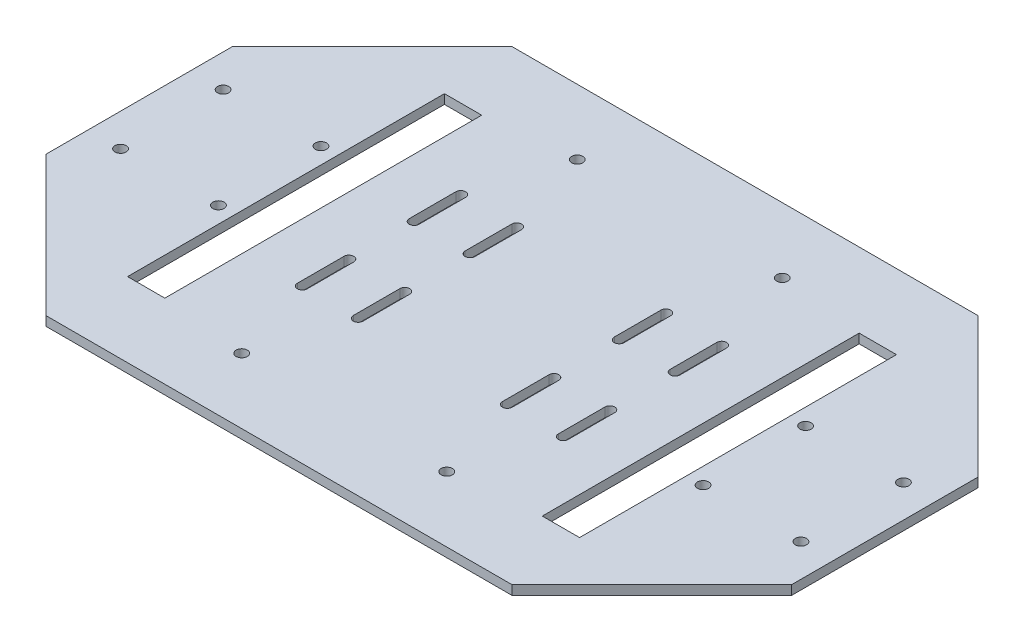
SolidWorks part; units mm, degrees
material "Pin"
ref_plane "Plan de face" through (0, 0, 0) normal (0, 0, 1) x (1, 0, 0)
ref_plane "Plan de dessus" through (0, 0, 0) normal (0, 1, 0) x (1, 0, 0)
ref_plane "Plan de droite" through (0, 0, 0) normal (1, 0, 0) x (0, 0, -1)
sketch "Esquisse1" plane through (0, 0, 0) normal (0, 1, 0) x (1, 0, 0)
  line L1 (0, 0) -> (160, 0)
  line L2 (0, 0) -> (0, 100)
  line L3 (0, 100) -> (160, 100)
  line L4 (160, 0) -> (160, 100)
  dimension "D1" = 100
  dimension "D2" = 160
extrude "Boss.-Extru.1" add sketch "Esquisse1" along normal blind 2
sketch "Esquisse2" plane through (0, 2, 0) normal (0, 1, 0) x (1, 0, 0)
  line L0 (30, 0) -> (0, 30)
  line L1 (0, 0) -> (160, 0) construction
  line L2 (0, 100) -> (0, 0) construction
  line L3 (0, 30) -> (0, 0)
  line L4 (0, 0) -> (30, 0)
  line L5 (30, 100) -> (0, 70)
  line L6 (160, 100) -> (0, 100) construction
  line L7 (0, 70) -> (0, 100)
  line L8 (0, 100) -> (30, 100)
  line L9 (130, 0) -> (160, 30)
  line L10 (160, 0) -> (160, 100) construction
  line L11 (160, 30) -> (160, 0)
  line L12 (160, 0) -> (130, 0)
  line L13 (130, 100) -> (160, 100)
  line L14 (160, 100) -> (160, 70)
  line L15 (160, 70) -> (130, 100)
  dimension "D1" = 30
  dimension "D2" = 30
  dimension "D3" = 30
  dimension "D4" = 30
  dimension "D5" = 30
  dimension "D6" = 30
  dimension "D7" = 30
  dimension "D8" = 30
extrude "Enlèv. mat.-Extru.1" cut sketch "Esquisse2" against normal blind 2
sketch "Esquisse3" plane through (0, 2, 0) normal (0, 1, 0) x (1, 0, 0)
  line L0 (-11.4853, 50) -> (207.2024, 50) construction
  line L1 (30, 0) -> (130, 0) construction
  line L2 (80, 141.5747) -> (80, -38.3594) construction
  line L3 (130, 100) -> (30, 100) construction
  line L4 (0, 70) -> (0, 30) construction
  line L5 (64, 43) -> (64, 33) construction
  line L6 (65.05, 43) -> (65.05, 33)
  line L7 (62.95, 43) -> (62.95, 33)
  line L8 (52, 33) -> (52, 43) construction
  line L9 (50.95, 33) -> (50.95, 43)
  line L10 (53.05, 33) -> (53.05, 43)
  line L11 (108, 33) -> (108, 43) construction
  line L12 (109.05, 33) -> (109.05, 43)
  line L13 (106.95, 33) -> (106.95, 43)
  line L14 (96, 43) -> (96, 33) construction
  line L15 (94.95, 43) -> (94.95, 33)
  line L16 (97.05, 43) -> (97.05, 33)
  line L17 (52, 67) -> (52, 57) construction
  line L18 (50.95, 67) -> (50.95, 57)
  line L19 (53.05, 67) -> (53.05, 57)
  line L20 (64, 57) -> (64, 67) construction
  line L21 (65.05, 57) -> (65.05, 67)
  line L22 (62.95, 57) -> (62.95, 67)
  line L23 (96, 57) -> (96, 67) construction
  line L24 (94.95, 57) -> (94.95, 67)
  line L25 (97.05, 57) -> (97.05, 67)
  line L26 (108, 67) -> (108, 57) construction
  line L27 (109.05, 67) -> (109.05, 57)
  line L28 (106.95, 67) -> (106.95, 57)
  arc A0 (65.05, 43) -> (62.95, 43) centre (64, 43) ccw
  arc A1 (62.95, 33) -> (65.05, 33) centre (64, 33) ccw
  arc A2 (50.95, 33) -> (53.05, 33) centre (52, 33) ccw
  arc A3 (53.05, 43) -> (50.95, 43) centre (52, 43) ccw
  arc A4 (109.05, 33) -> (106.95, 33) centre (108, 33) cw
  arc A5 (106.95, 43) -> (109.05, 43) centre (108, 43) cw
  arc A6 (94.95, 43) -> (97.05, 43) centre (96, 43) cw
  arc A7 (97.05, 33) -> (94.95, 33) centre (96, 33) cw
  arc A8 (50.95, 67) -> (53.05, 67) centre (52, 67) cw
  arc A9 (53.05, 57) -> (50.95, 57) centre (52, 57) cw
  arc A10 (65.05, 57) -> (62.95, 57) centre (64, 57) cw
  arc A11 (62.95, 67) -> (65.05, 67) centre (64, 67) cw
  arc A12 (94.95, 57) -> (97.05, 57) centre (96, 57) ccw
  arc A13 (97.05, 67) -> (94.95, 67) centre (96, 67) ccw
  arc A14 (109.05, 67) -> (106.95, 67) centre (108, 67) ccw
  arc A15 (106.95, 57) -> (109.05, 57) centre (108, 57) ccw
  point P12 (64, 38)
  point P17 (52, 38)
  point P26 (108, 38)
  point P33 (96, 38)
  point P40 (52, 62)
  point P47 (64, 62)
  point P54 (96, 62)
  point P61 (108, 62)
  dimension "D1" = 50
  dimension "D2" = 80
  dimension "D3" = 10
  dimension "D4" = 10
  dimension "D5" = 2.1
  dimension "D6" = 2.1
  dimension "D7" = 12
  dimension "D8" = 12
  dimension "D9" = 12
  dimension "D10" = 16
extrude "Enlèv. mat.-Extru.2" cut sketch "Esquisse3" against normal blind 2
hole_wizard "Dégagement M21" positions "Esquisse4" profile "Esquisse5" size "M2" standard "ISO" slot yes end condition up to next
sketch "Esquisse4" plane through (0, 2, 0) normal (0, 1, 0) x (1, 0, 0)
  point P0 (28, 39)
  point P3 (28, 61)
  point P6 (7, 61)
  point P9 (7, 39)
sketch "Esquisse5" plane through (28, 2, -39) normal (1, 0, 0) x (0, 0, 1)
  line L0 (0, 0) -> (0, 2.001)
  line L1 (0, 2.001) -> (1.2, 2.001)
  line L2 (1.2, 2.001) -> (1.2, 0)
  line L5 (1.2, 0) -> (0, 0)
  line L11 (0, -6.35) -> (0, 107.95) construction
  dimension "Diamètre du perçage jusqu'au prochain" = 2.4
  dimension "Profondeur du perçage jusqu'au prochain" = 2.001
hole_wizard "Dégagement M22" positions "Esquisse6" profile "Esquisse7" size "M2" standard "ISO" slot yes end condition up to next
sketch "Esquisse6" plane through (0, 2, 0) normal (0, 1, 0) x (1, 0, 0)
  point P0 (58, 14)
  point P3 (58, 86)
sketch "Esquisse7" plane through (58, 2, -14) normal (1, 0, 0) x (0, 0, 1)
  line L0 (0, 0) -> (0, 2.001)
  line L1 (0, 2.001) -> (1.2, 2.001)
  line L2 (1.2, 2.001) -> (1.2, 0)
  line L5 (1.2, 0) -> (0, 0)
  line L11 (0, -6.35) -> (0, 107.95) construction
  dimension "Diamètre du perçage jusqu'au prochain" = 2.4
  dimension "Profondeur du perçage jusqu'au prochain" = 2.001
ref_plane "Plan8" through (80, 0, 0) normal (-1, 0, 0) x (0, 0, 1)
mirror "Symétrie1" about plane through (80, 0, 0) normal (-1, 0, 0) of "Dégagement M22", "Dégagement M21"
sketch "Esquisse11" plane through (0, 2, 0) normal (0, 1, 0) x (1, 0, 0)
  line L0 (0, 70) -> (0, 30) construction
  line L1 (31.5, 84) -> (39.5, 84)
  line L2 (31.5, 84) -> (31.5, 16)
  line L3 (31.5, 16) -> (39.5, 16)
  line L4 (39.5, 84) -> (39.5, 16)
  line L5 (30, 0) -> (130, 0) construction
  line L6 (130, 100) -> (30, 100) construction
  line L7 (80, 111.4033) -> (80, -12.0266) construction
  line L8 (128.5, 16) -> (120.5, 16)
  line L9 (120.5, 84) -> (120.5, 16)
  line L10 (128.5, 84) -> (120.5, 84)
  line L11 (128.5, 84) -> (128.5, 16)
  dimension "D1" = 8
  dimension "D2" = 31.5
  dimension "D3" = 16
  dimension "D4" = 16
  dimension "D5" = 80
extrude "Enlèv. mat.-Extru.5" cut sketch "Esquisse11" against normal up to next and the other way through all
